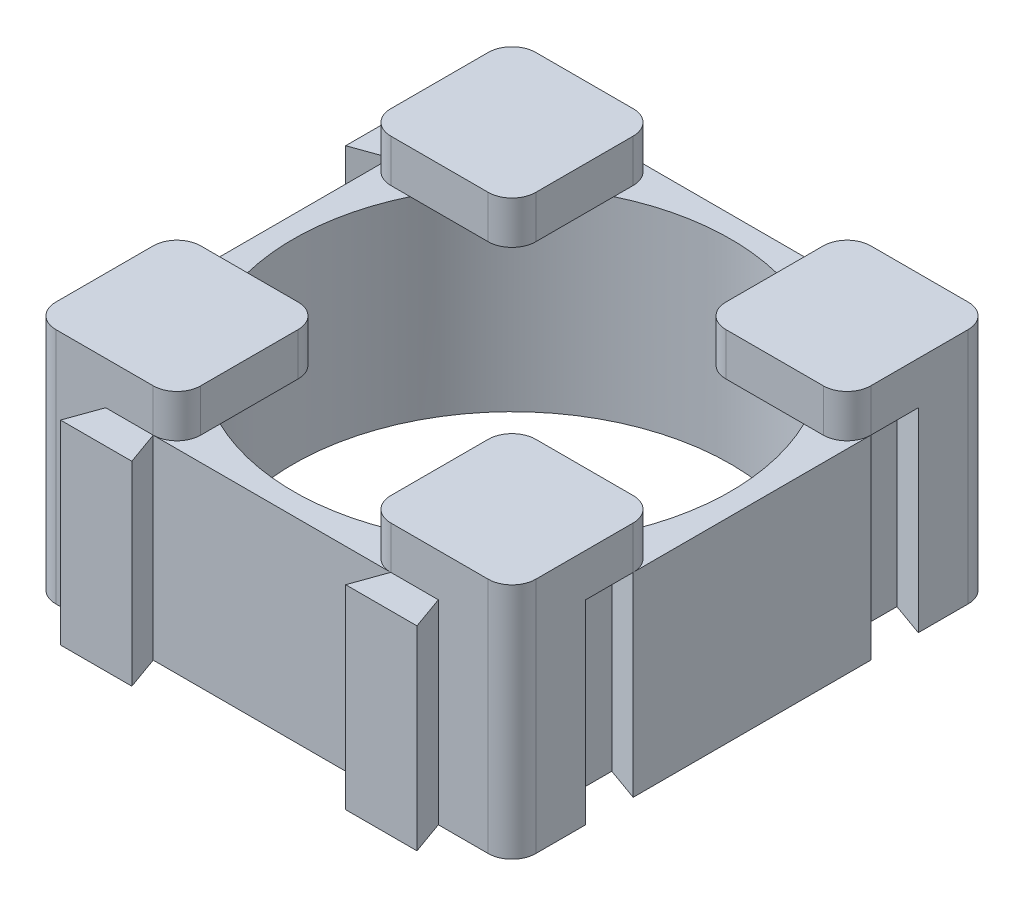
SolidWorks part; units mm, degrees
material "ABS"
ref_plane "Front Plane" through (0, 0, 0) normal (0, 0, 1) x (1, 0, 0)
ref_plane "Top Plane" through (0, 0, 0) normal (0, 1, 0) x (1, 0, 0)
ref_plane "Right Plane" through (0, 0, 0) normal (1, 0, 0) x (0, 0, -1)
sketch "Sketch1" plane through (0, 0, 0) normal (0, 1, 0) x (1, 0, 0)
  line L0 (-14.0032, 0) -> (15.5031, 0) construction
  line L1 (-9.1, 10.1) -> (-7, 10.1)
  line L2 (-10.1, 9.1) -> (-10.1, 7)
  line L3 (-9.1, -10.1) -> (-7, -10.1)
  line L4 (10.1, 9.1) -> (10.1, 7)
  line L5 (0, 12.8597) -> (0, -11.7289) construction
  line L6 (-10.1, 7) -> (-11.5, 7.5)
  line L7 (-11.5, 7.5) -> (-11.5, 4.5)
  line L8 (-11.5, 4.5) -> (-10.1, 5)
  line L9 (10.1, 7) -> (8.7, 7.5)
  line L10 (8.7, 7.5) -> (8.7, 4.5)
  line L11 (8.7, 4.5) -> (10.1, 5)
  line L12 (-10.1, 5) -> (-10.1, -5)
  line L13 (10.1, 5) -> (10.1, -5)
  line L14 (7, 10.1) -> (7.5, 8.7)
  line L15 (7.5, 8.7) -> (4.5, 8.7)
  line L16 (4.5, 8.7) -> (5, 10.1)
  line L17 (7, 10.1) -> (9.1, 10.1)
  line L18 (-7, -10.1) -> (-7.5, -11.5)
  line L19 (-7.5, -11.5) -> (-4.5, -11.5)
  line L20 (-4.5, -11.5) -> (-5, -10.1)
  line L21 (-5, -10.1) -> (5, -10.1)
  line L22 (-11.5, -4.5) -> (-10.1, -5)
  line L23 (-11.5, -7.5) -> (-11.5, -4.5)
  line L24 (-10.1, -7) -> (-11.5, -7.5)
  line L25 (-10.1, -7) -> (-10.1, -9.1)
  line L26 (4.5, -11.5) -> (5, -10.1)
  line L27 (7.5, -11.5) -> (4.5, -11.5)
  line L28 (7, -10.1) -> (7.5, -11.5)
  line L29 (7, -10.1) -> (9.1, -10.1)
  line L30 (-4.5, 8.7) -> (-5, 10.1)
  line L31 (-7.5, 8.7) -> (-4.5, 8.7)
  line L32 (-7, 10.1) -> (-7.5, 8.7)
  line L33 (-5, 10.1) -> (5, 10.1)
  line L34 (8.7, -4.5) -> (10.1, -5)
  line L35 (8.7, -7.5) -> (8.7, -4.5)
  line L36 (10.1, -7) -> (8.7, -7.5)
  line L37 (10.1, -7) -> (10.1, -9.1)
  arc A0 (-10.1, -9.1) -> (-9.1, -10.1) centre (-9.1, -9.1) ccw
  arc A1 (9.1, -10.1) -> (10.1, -9.1) centre (9.1, -9.1) ccw
  arc A2 (9.1, 10.1) -> (10.1, 9.1) centre (9.1, 9.1) cw
  arc A3 (-9.1, 10.1) -> (-10.1, 9.1) centre (-9.1, 9.1) ccw
  circle A4 centre (0, 0) radius 9.2
  point P7 (-10.1, -10.1)
  point P10 (10.1, -10.1)
  point P13 (10.1, 10.1)
  dimension "D5" = 1
  dimension "D6" = 18.4
  dimension "D1" = 20.2
  dimension "D2" = 20.2
  dimension "D3" = 10.1
  dimension "D4" = 10.1
  dimension "D7" = 1.4
  dimension "D8" = 1.4
  dimension "D9" = 3
  dimension "D10" = 3
  dimension "D11" = 2
  dimension "D12" = 0.5
  dimension "D13" = 4.5
  dimension "D14" = 2
  dimension "D15" = 3
  dimension "D16" = 0.5
  dimension "D17" = 4.5
  dimension "D18" = 1.4
  dimension "D19" = 3
  dimension "D20" = 2
  dimension "D21" = 0.5
  dimension "D22" = 1.4
  dimension "D23" = 4.5
extrude "Boss-Extrude1" add sketch "Sketch1" along normal blind 8.2
sketch "Sketch2" plane through (0, 8.2, 0) normal (0, 1, 0) x (1, 0, 0)
  line L0 (-9.1, 4) -> (-5, 4)
  line L1 (-10.1, 5) -> (-10.1, -5) construction
  line L2 (-4, 5) -> (-4, 9.1)
  line L3 (5, 10.1) -> (-5, 10.1) construction
  line L4 (-5, 10.1) -> (-9.1, 10.1)
  line L5 (-10.1, 9.1) -> (-10.1, 5)
  line L6 (0, 2.2334) -> (0, -2.7823) construction
  line L7 (-2.0812, 0) -> (2.2435, 0) construction
  line L8 (10.1, 9.1) -> (10.1, 5)
  line L9 (5, 10.1) -> (9.1, 10.1)
  line L10 (4, 5) -> (4, 9.1)
  line L11 (9.1, 4) -> (5, 4)
  line L12 (9.1, -4) -> (5, -4)
  line L13 (10.1, -9.1) -> (10.1, -5)
  line L14 (5, -10.1) -> (9.1, -10.1)
  line L15 (4, -5) -> (4, -9.1)
  line L16 (-4, -5) -> (-4, -9.1)
  line L17 (-5, -10.1) -> (-9.1, -10.1)
  line L18 (-10.1, -9.1) -> (-10.1, -5)
  line L19 (-9.1, -4) -> (-5, -4)
  arc A0 (-4, 9.1) -> (-5, 10.1) centre (-5, 9.1) ccw
  arc A1 (-5, 4) -> (-4, 5) centre (-5, 5) ccw
  arc A2 (-9.1, 4) -> (-10.1, 5) centre (-9.1, 5) cw
  arc A3 (-9.1, 10.1) -> (-10.1, 9.1) centre (-9.1, 9.1) ccw
  arc A4 (9.1, 10.1) -> (10.1, 9.1) centre (9.1, 9.1) cw
  arc A5 (4, 9.1) -> (5, 10.1) centre (5, 9.1) cw
  arc A6 (5, 4) -> (4, 5) centre (5, 5) cw
  arc A7 (9.1, 4) -> (10.1, 5) centre (9.1, 5) ccw
  arc A8 (5, -4) -> (4, -5) centre (5, -5) ccw
  arc A9 (9.1, -4) -> (10.1, -5) centre (9.1, -5) cw
  arc A10 (9.1, -10.1) -> (10.1, -9.1) centre (9.1, -9.1) ccw
  arc A11 (4, -9.1) -> (5, -10.1) centre (5, -9.1) ccw
  arc A12 (-5, -4) -> (-4, -5) centre (-5, -5) cw
  arc A13 (-4, -9.1) -> (-5, -10.1) centre (-5, -9.1) cw
  arc A14 (-9.1, -10.1) -> (-10.1, -9.1) centre (-9.1, -9.1) cw
  arc A15 (-9.1, -4) -> (-10.1, -5) centre (-9.1, -5) ccw
  point P10 (-4, 10.1)
  point P13 (-4, 4)
  point P16 (-10.1, 4)
  dimension "D3" = 1
  dimension "D1" = 6.1
  dimension "D2" = 6.1
extrude "Boss-Extrude2" add sketch "Sketch2" along normal blind 1.8
